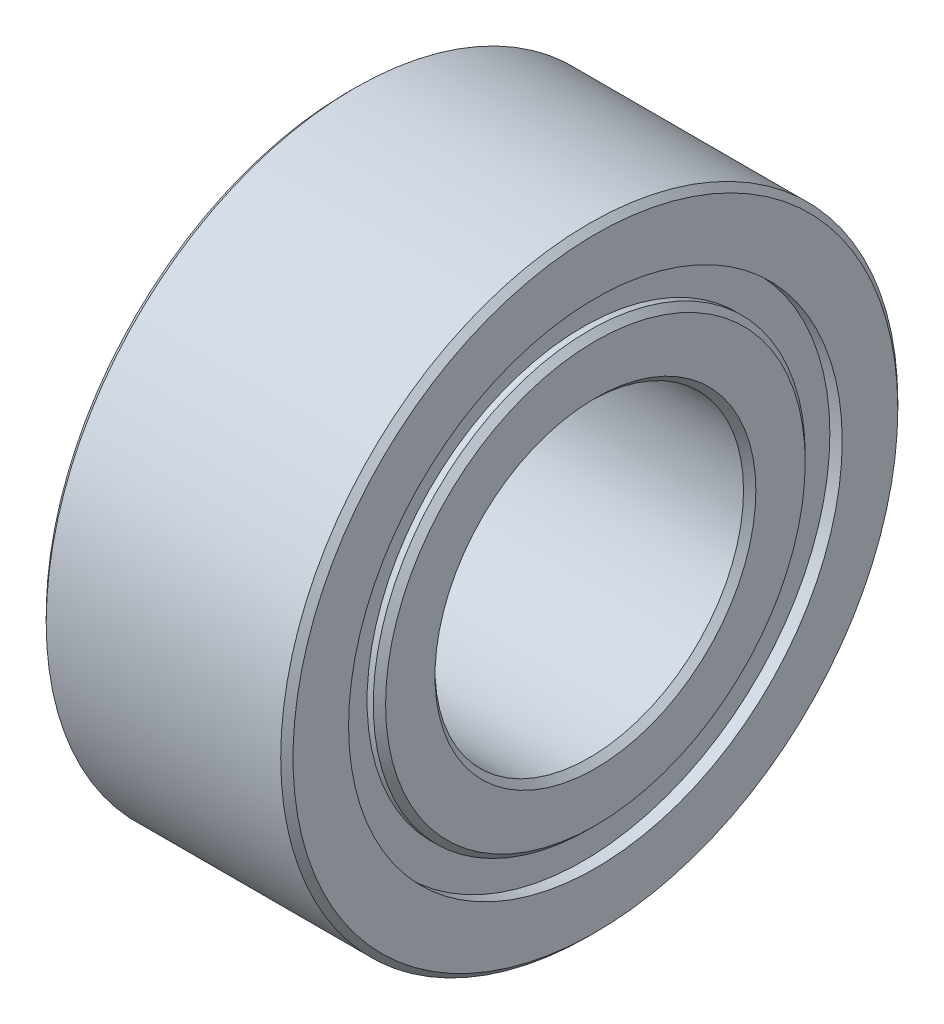
SolidWorks part; units mm, degrees
ref_plane "前视基准面" through (0, 0, 0) normal (0, 0, 1) x (1, 0, 0)
ref_plane "上视基准面" through (0, 0, 0) normal (0, 1, 0) x (1, 0, 0)
ref_plane "右视基准面" through (0, 0, 0) normal (1, 0, 0) x (0, 0, -1)
sketch "草图1" plane through (0, 0, 0) normal (1, 0, 0) x (0, 0, -1)
  circle A0 centre (0, 0) radius 2.5
  circle A1 centre (0, 0) radius 5
  dimension "D1" = 5
  dimension "D2" = 10
extrude "凸台-拉伸1" add sketch "草图1" along normal blind 4
sketch "草图2" plane through (4, 0, 0) normal (1, 0, 0) x (0, 0, -1)
  circle A0 centre (-0.0004, 0) radius 3.5
  circle A1 centre (-0.0004, 0) radius 3.9996
  circle A2 centre (0, 0) radius 5 construction
  dimension "D1" = 1
  dimension "D2" = 7
extrude "切除-拉伸1" cut sketch "草图2" against normal blind 0.2
sketch "草图3" plane through (0, 0, 0) normal (-1, 0, 0) x (0, 0, 1)
  circle A0 centre (-0.0491, 0) radius 3.5
  circle A1 centre (-0.0491, 0) radius 3.9509
  circle A2 centre (0, 0) radius 5 construction
  dimension "D1" = 7
  dimension "D2" = 1
extrude "切除-拉伸2" cut sketch "草图3" against normal blind 0.2
chamfer "倒角1" distance 0.1 angle 45 7 edges at (4, 0, -5) (4, 0, -2.5) (4, 0, -3.4996) (0, 0, -5) (0, 0, 3.9018) (0, 0, -2.5) (0, 0, 3.4509)
